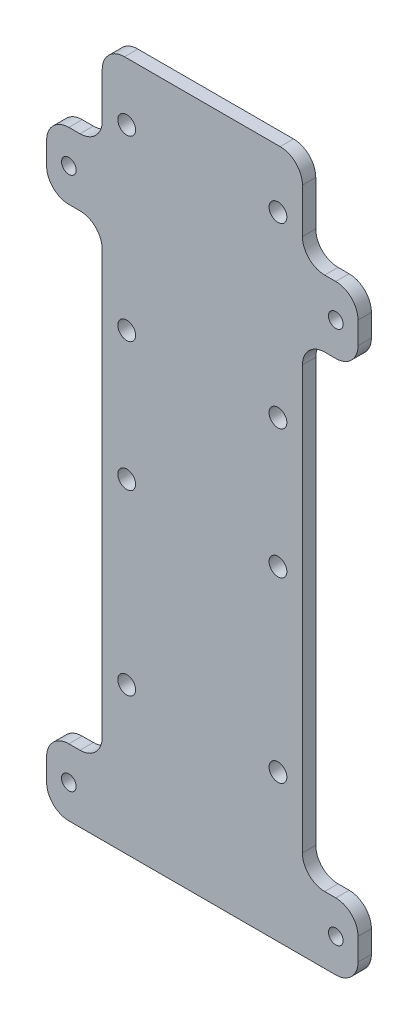
SolidWorks part; units mm, degrees
material "3.1325 (EN-AW 2017A)"
ref_plane "正面" through (0, 0, 0) normal (0, 0, 1) x (1, 0, 0)
ref_plane "平面" through (0, 0, 0) normal (0, 1, 0) x (1, 0, 0)
ref_plane "右側面" through (0, 0, 0) normal (1, 0, 0) x (0, 0, -1)
sketch "ｽｹｯﾁ1" plane through (0, 0, 0) normal (0, 0, 1) x (1, 0, 0)
  line L1 (-35, -77.5) -> (35, -77.5)
  line L2 (-35, -77.5) -> (-35, 77.5)
  line L3 (-35, 77.5) -> (35, 77.5)
  line L4 (35, -77.5) -> (35, 77.5)
  line L5 (-35, -77.5) -> (35, 77.5) construction
  line L6 (-35, 77.5) -> (35, -77.5) construction
  dimension "D1" = 70
  dimension "D2" = 155
extrude "ﾎﾞｽ - 押し出し1" add sketch "ｽｹｯﾁ1" along normal blind 3
sketch "ｽｹｯﾁ2" plane through (0, 0, 3) normal (0, 0, 1) x (1, 0, 0)
  line L0 (35, -77.5) -> (35, 77.5) construction
  line L6 (-35, -77.5) -> (35, -77.5) construction
  line L7 (-35, -77.5) -> (-35, 77.5) construction
  line L8 (-35, 77.5) -> (35, 77.5) construction
  circle A4 centre (-17, -44.5) radius 2
  circle A5 centre (17, -44.5) radius 2
  circle A6 centre (17, -4.5) radius 2
  circle A7 centre (-17, -4.5) radius 2
  circle A8 centre (-17, 24.5) radius 2
  circle A9 centre (-17, 64.5) radius 2
  circle A10 centre (17, 64.5) radius 2
  circle A11 centre (17, 24.5) radius 2
  circle A12 centre (-30, -70) radius 1.65
  circle A13 centre (30, -70) radius 1.65
  circle A14 centre (30, 50) radius 1.65
  circle A15 centre (-30, 50) radius 1.65
  point P2 (0, -77.5)
  dimension "D2" = 17
  dimension "D6" = 3.3
  dimension "D7" = 7.5
  dimension "D9" = 4
  dimension "D10" = 2
  dimension "D11" = 2
  dimension "D14" = 40
  dimension "D16" = 5
  dimension "D3" = 29
  dimension "D4" = 17
  dimension "D5" = 13
  dimension "D8" = 5
  dimension "D18" = 120
  dimension "D15" = 34
  dimension "D19" = 5
  dimension "D12" = 2
  dimension "D13" = 2
  dimension "D17" = 2
extrude "ｶｯﾄ - 押し出し1" cut sketch "ｽｹｯﾁ2" against normal blind 3
sketch "ｽｹｯﾁ3" plane through (0, 0, 3) normal (0, 0, 1) x (1, 0, 0)
  line L0 (-35, -77.5) -> (-35, 77.5) construction
  line L1 (-35, 42.5) -> (-22.5, 42.5)
  line L2 (-35, 42.5) -> (-35, -62.5)
  line L3 (-35, -62.5) -> (-22.5, -62.5)
  line L4 (-22.5, 42.5) -> (-22.5, -62.5)
  line L5 (35, -77.5) -> (35, 77.5) construction
  line L6 (35, -62.5) -> (22.5, -62.5)
  line L7 (35, -62.5) -> (35, 42.5)
  line L8 (35, 42.5) -> (22.5, 42.5)
  line L9 (22.5, -62.5) -> (22.5, 42.5)
  line L11 (-35, -77.5) -> (35, -77.5) construction
  line L13 (-35, 77.5) -> (-22.5, 77.5)
  line L14 (-35, 77.5) -> (-35, 57.5)
  line L15 (-35, 57.5) -> (-22.5, 57.5)
  line L16 (-22.5, 77.5) -> (-22.5, 57.5)
  line L17 (35, 77.5) -> (22.5, 77.5)
  line L18 (35, 77.5) -> (35, 57.5)
  line L19 (35, 57.5) -> (22.5, 57.5)
  line L20 (22.5, 77.5) -> (22.5, 57.5)
  circle A0 centre (-30, 50) radius 1.65 construction
  dimension "D1" = 7.5
  dimension "D2" = 22.5
  dimension "D3" = 22.5
  dimension "D4" = 15
  dimension "D5" = 15
  dimension "D6" = 15
extrude "ｶｯﾄ - 押し出し2" cut sketch "ｽｹｯﾁ3" against normal blind 10
fillet "ﾌｨﾚｯﾄ1" radius 5 16 edges at (35, -77.5, 1.5) (-35, -77.5, 1.5) (35, -62.5, 1.5) (22.5, -62.5, 1.5) (-22.5, -62.5, 1.5) (-35, -62.5, 1.5) (-22.5, 42.5, 1.5) (22.5, 42.5, 1.5) (35, 42.5, 1.5) (-35, 42.5, 1.5) (-22.5, 57.5, 1.5) (35, 57.5, 1.5) (22.5, 57.5, 1.5) (22.5, 77.5, 1.5) (-22.5, 77.5, 1.5) (-35, 57.5, 1.5)
